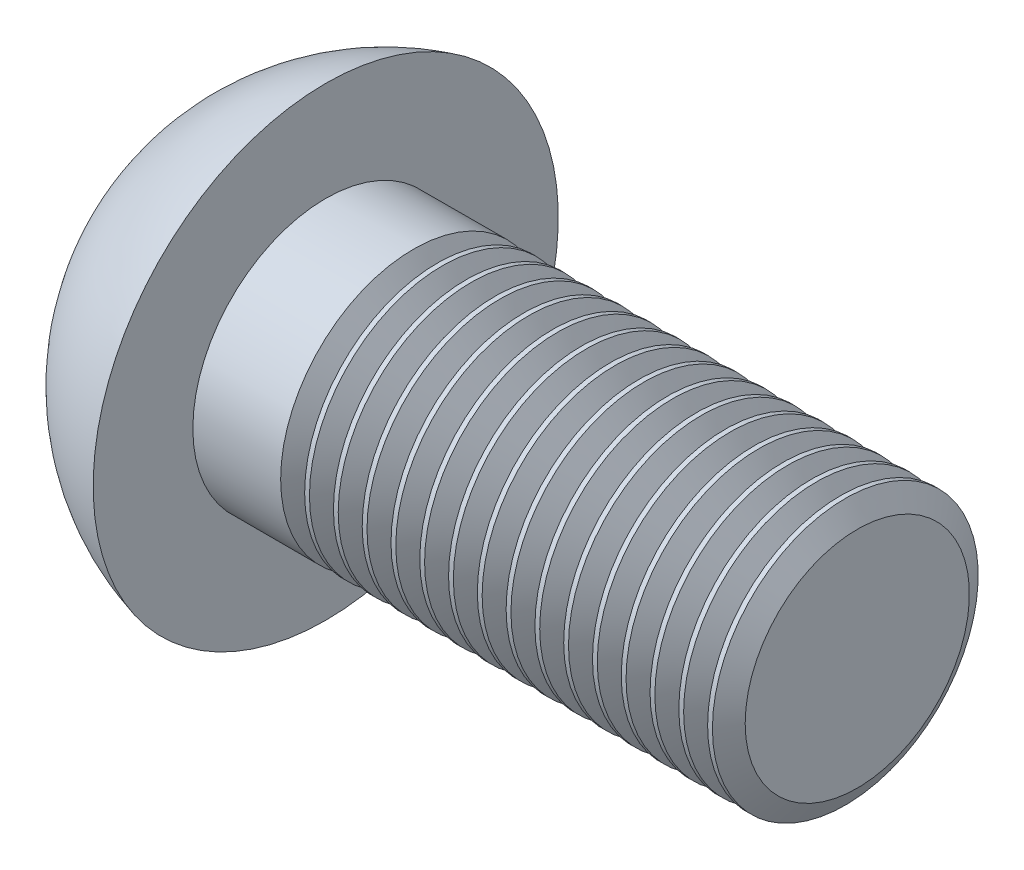
SolidWorks part; units mm, degrees
ref_plane "Front" through (0, 0, 0) normal (0, 0, 1) x (1, 0, 0)
ref_plane "Top" through (0, 0, 0) normal (0, 1, 0) x (1, 0, 0)
ref_plane "Right" through (0, 0, 0) normal (1, 0, 0) x (0, 0, -1)
sketch "Sketch1" plane through (0, 0, 0) normal (1, 0, 0) x (0, 0, -1)
  line L0 (0, 0) -> (2, 0) construction
  circle A0 centre (0, 0) radius 5.25
  dimension "dk" = 10.5
  dimension "a" = 2
extrude "BaseHead" add sketch "Sketch1" along normal blind 3.3
sketch "Sketch2" plane through (3.3, 0, 0) normal (1, 0, 0) x (0, 0, -1)
  circle A0 centre (0, 0) radius 3
  dimension "d" = 6
extrude "BaseBody" add sketch "Sketch2" along normal blind 12
cosmetic thread "ThreadCosmetic1" [suppressed] parameters "D1"=10, "THD_MINOR"=4.917
fillet "HeadFillet" [suppressed] radius 0.25
sketch "Sketch3" plane through (-13.4796, 2.4796, 0) normal (0, 0, 1) x (0, -1, 0)
  line L0 (2.4796, 13.4796) -> (2.4796, 41.0387) construction
  line L3 (-2.7704, 13.4796) -> (2.4796, 13.4796) construction
  line L5 (-7.7704, 16.7796) -> (-7.7704, 8.4796)
  line L6 (-0.3104, 13.4796) -> (-0.3104, 8.4796)
  line L7 (-0.3104, 8.4796) -> (-7.7704, 8.4796)
  line L8 (-7.7704, 16.7796) -> (-2.7704, 16.7796)
  line L9 (-2.7704, 13.4796) -> (7.7296, 13.4796) construction
  arc A0 (-2.7704, 16.7796) -> (-0.3104, 13.4796) centre (2.4796, 18.1263) ccw
  dimension "D2" = 5
  dimension "e" = 5.58
  dimension "D3" = 5
revolve "Cut-Revolve1" cut sketch "Sketch3" angle 360 about L0
sketch "Sketch4" plane through (0, 0, 0) normal (1, 0, 0) x (0, 0, -1)
  line L1 (2.3094, 0) -> (1.1547, 2)
  line L2 (1.1547, 2) -> (-1.1547, 2)
  line L3 (-1.1547, 2) -> (-2.3094, 0)
  line L4 (-2.3094, 0) -> (-1.1547, -2)
  line L5 (-1.1547, -2) -> (1.1547, -2)
  line L6 (1.1547, -2) -> (2.3094, 0)
  circle A0 centre (0, 0) radius 2 construction
  dimension "s" = 4
extrude "HexagonSocket" cut sketch "Sketch4" along normal blind 2.08
sketch "Sketch5" plane through (2.08, 0, 0) normal (-1, 0, 0) x (0, 0, 1)
  line L0 (1.1547, -2) -> (-1.1547, -2) construction
  line L1 (-1.1547, -2) -> (-2.3094, 0) construction
  line L2 (2.3094, 0) -> (1.1547, -2) construction
  line L3 (1.1547, 2) -> (2.3094, 0) construction
  line L4 (-2.3094, 0) -> (-1.1547, 2) construction
  line L5 (-1.1547, 2) -> (1.1547, 2) construction
  line L6 (1.1547, -2) -> (-1.1547, -2)
  line L7 (-1.1547, -2) -> (-2.3094, 0)
  line L8 (2.3094, 0) -> (1.1547, -2)
  line L9 (1.1547, 2) -> (2.3094, 0)
  line L10 (-2.3094, 0) -> (-1.1547, 2)
  line L11 (-1.1547, 2) -> (1.1547, 2)
extrude "Cut-Extrude2" cut sketch "Sketch5" against normal blind 5 draft 60
sketch "Sketch6" plane through (0, 0, 0) normal (0, 0, 1) x (1, 0, 0)
  line L0 (15.3, 2.531) -> (15.5708, 3)
  line L1 (15.5708, 3) -> (15.5708, 3.5415)
  line L2 (15.5708, 3.5415) -> (15.0293, 3.5415)
  line L3 (15.0293, 3.5415) -> (15.0293, 3)
  line L4 (15.0293, 3) -> (15.3, 2.531)
  line L5 (0, 0) -> (24.7294, 0) construction
  line L6 (15.3, -3) -> (15.3, 3) construction
  dimension "D1" = 0.5415
  dimension "D2" = 6
revolve "Cut-Revolve10" cut sketch "Sketch6" angle 360 about L5
pattern_linear "LPattern10" count 16 spacing 0.6498 along (-1, 0, 0) of "Cut-Revolve10"
equation "\"D1@ThreadCosmetic1\" = \"l@BaseBody\" - \"a@Sketch1\""
equation "\"D2@Sketch6\" = \"d@Sketch2\""
equation "\"D1@Sketch6\" =  (\"d@Sketch2\" - \"THD_MINOR@ThreadCosmetic1\" )  / 2"
equation "\"D3@LPattern10\" = \"D1@Sketch6\" * 1.2"
equation "\"D1@LPattern10\" = \"D1@ThreadCosmetic1\" / \"D3@LPattern10\" + 1"
